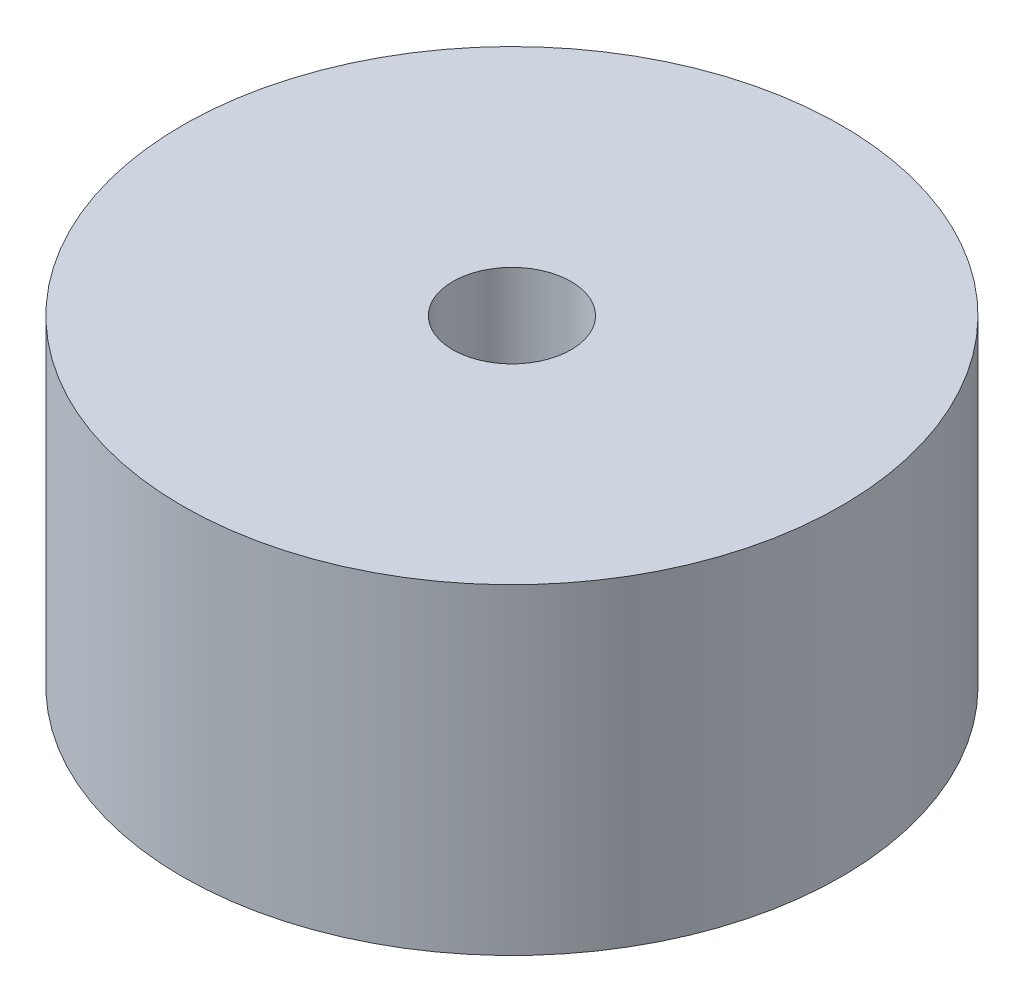
SolidWorks part; units mm, degrees
material "AISI 1045 Steel, cold drawn"
ref_plane "Front Plane" through (0, 0, 0) normal (0, 0, 1) x (1, 0, 0)
ref_plane "Top Plane" through (0, 0, 0) normal (0, 1, 0) x (1, 0, 0)
ref_plane "Right Plane" through (0, 0, 0) normal (1, 0, 0) x (0, 0, -1)
sketch "Sketch1" plane through (0, 0, 0) normal (0, 1, 0) x (1, 0, 0)
  circle A0 centre (0, 0) radius 19.5
  circle A1 centre (0, 0) radius 3.5
  dimension "D1" = 7
  dimension "D2" = 39
extrude "Boss-Extrude1" add sketch "Sketch1" along normal blind 19
